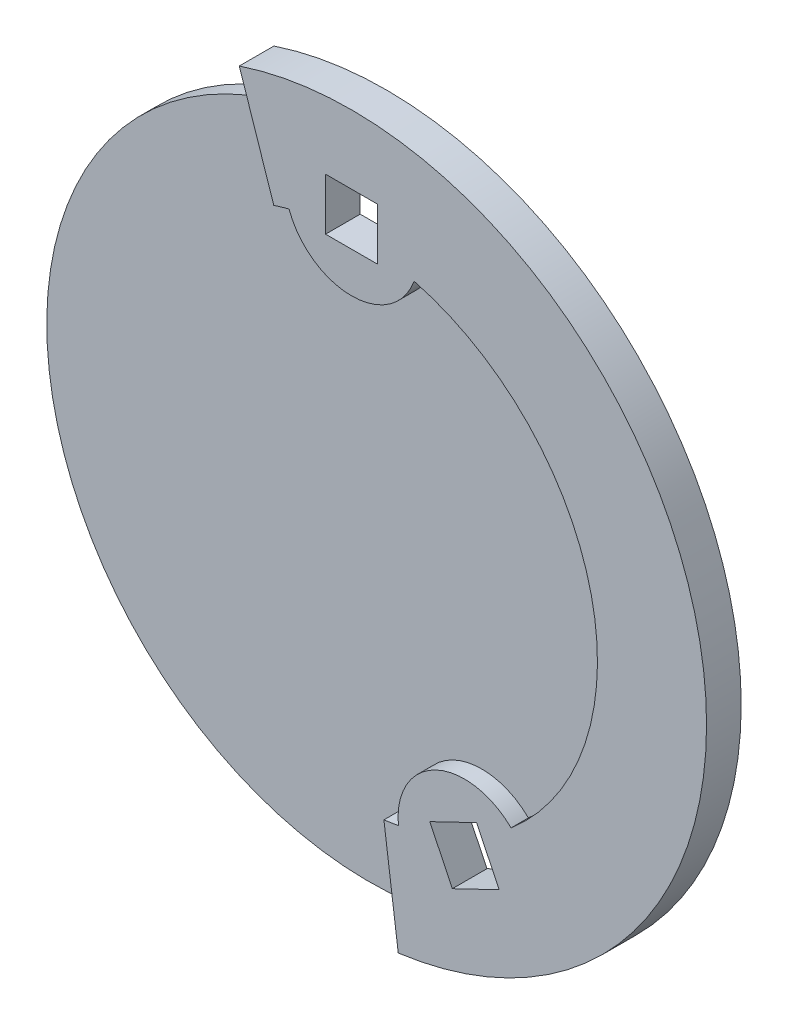
SolidWorks part; units mm, degrees
ref_plane "Plano frontal" through (0, 0, 0) normal (0, 0, 1) x (1, 0, 0)
ref_plane "Plano superior" through (0, 0, 0) normal (0, 1, 0) x (1, 0, 0)
ref_plane "Plano direito" through (0, 0, 0) normal (1, 0, 0) x (0, 0, -1)
sketch "Esboço1" plane through (0, 0, 0) normal (0, 0, 1) x (1, 0, 0)
  line L0 (-5.882, 17.6454) -> (-6.4829, 19.4479)
  line L1 (2.3565, -18.4501) -> (2.5973, -20.3348)
  line L4 (-8.3, 14.376) -> (-10.25, 17.7535) construction
  line L5 (-6.4829, 19.4479) -> (-5.882, 17.6454) construction
  arc A0 (2.5973, -20.3348) -> (-6.4829, 19.4479) centre (0, 0) ccw
  arc A2 (-5.882, 17.6454) -> (2.3565, -18.4501) centre (0, 0) ccw
  arc A17 (-3.7927, 18.2092) -> (3.7927, 18.2092) centre (0, 16.6) ccw construction
  arc A19 (11.3178, -14.7603) -> (4.4835, -18.0515) centre (7.2025, -14.9561) ccw construction
  arc A21 (-5.6542, -15.6074) -> (1.2298, -9.6288) centre (-4.77, -9.6729) ccw construction
  arc A22 (-8.3, 14.376) -> (-5.6542, -15.6074) centre (0, 0) ccw construction
extrude "Ressalto-extrusão1" add sketch "Esboço1" along normal blind 1
sketch "Esboço2" plane through (0, 0, 1) normal (0, 0, 1) x (1, 0, 0)
  line L0 (-4.4906, 13.4712) -> (-6.4829, 19.4479)
  line L1 (1.868, -14.0766) -> (2.6967, -20.3219)
  line L10 (-1.5, 16.5292) -> (1.5, 13.5292) construction
  arc A0 (2.6967, -20.3219) -> (-6.4829, 19.4479) centre (0, 0) ccw
  arc A1 (1.868, -14.0766) -> (2.7063, -13.9397) centre (0, 0) ccw
  arc A2 (9.2112, -10.8071) -> (2.7063, -13.9397) centre (6.5209, -13.5408) ccw
  arc A3 (-3.6099, 13.7335) -> (3.6099, 13.7335) centre (0, 15.0292) ccw
  arc A4 (-3.6099, 13.7335) -> (-4.4906, 13.4712) centre (0, 0) ccw
  arc A5 (9.2112, -10.8071) -> (3.6099, 13.7335) centre (0, 0) ccw
extrude "Ressalto-extrusão2" add sketch "Esboço2" along normal blind 1
sketch "Esboço3" plane through (0, 0, 0) normal (0, 0, -1) x (-1, 0, 0)
  line L0 (0, 0) -> (0, 15.0292) construction
  line L1 (0, 15.0292) -> (-6.5209, -13.5408) construction
  line L2 (-6.5209, -13.5408) -> (-7.2215, -11.5386) construction
  line L3 (-7.2215, -11.5386) -> (-5.8203, -15.5431) construction
  line L4 (-5.8203, -15.5431) -> (-6.5209, -13.5408) construction
  line L5 (-7.2215, -11.5386) -> (-4.5186, -12.8402)
  line L6 (-4.5186, -12.8402) -> (-5.8203, -15.5431)
  line L7 (-5.8203, -15.5431) -> (-8.5232, -14.2415)
  line L8 (-8.5232, -14.2415) -> (-7.2215, -11.5386)
  line L9 (-1.5, 16.5292) -> (1.5, 16.5292)
  line L10 (1.5, 16.5292) -> (1.5, 13.5292)
  line L11 (1.5, 13.5292) -> (-1.5, 13.5292)
  line L12 (-1.5, 13.5292) -> (-1.5, 16.5292)
extrude "Corte-extrusão1" cut sketch "Esboço3" against normal through all
